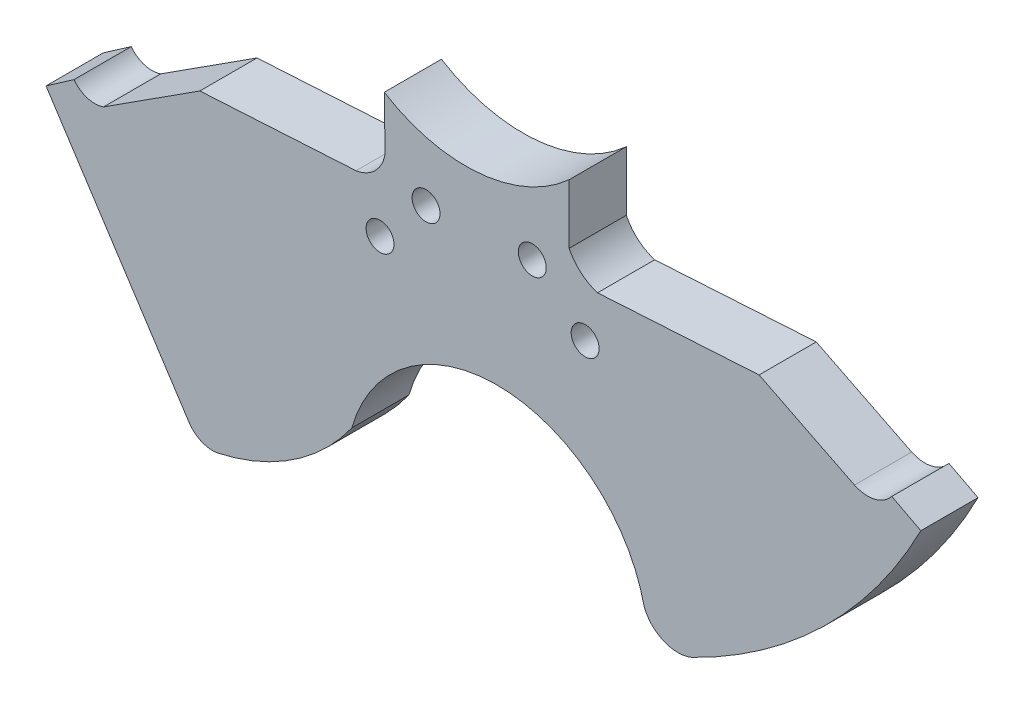
SolidWorks part; units mm, degrees
ref_plane "Plano frontal" through (0, 0, 0) normal (0, 0, 1) x (1, 0, 0)
ref_plane "Plano superior" through (0, 0, 0) normal (0, 1, 0) x (1, 0, 0)
ref_plane "Plano direito" through (0, 0, 0) normal (1, 0, 0) x (0, 0, -1)
sketch "Esboço1" plane through (0, 0, 0) normal (0, 0, 1) x (1, 0, 0)
  line L0 (80.0166, 93.0122) -> (121.8389, 95.564) construction
  line L1 (35.3852, 10.0755) -> (3.023, 59.8213)
  line L2 (121.9464, 97.8545) -> (121.9464, 100.8122)
  line L3 (79.93, 94.4157) -> (79.93, 97.029)
  line L4 (9.3896, 64.2413) -> (3.023, 59.8213)
  line L5 (16.1166, 62.2388) -> (37.9957, 76.3106)
  line L8 (37.9957, 76.3106) -> (73.5102, 78.3627)
  line L9 (79.93, 94.4157) -> (80.1405, 85.276)
  line L16 (121.9464, 87.3069) -> (121.9464, 97.8545)
  line L19 (128.4006, 81.7737) -> (165.136, 83.9713)
  line L21 (165.136, 83.9713) -> (186.825, 73.1367)
  line L22 (195.3054, 75.1425) -> (201.9046, 71.6896)
  line L29 (35.6621, 9.6499) -> (35.3852, 10.0755)
  arc A0 (139.0206, 25.2485) -> (72.5465, 27.2443) centre (105.5339, 17.9302) ccw
  arc A1 (79.93, 94.4157) -> (121.9464, 97.8545) centre (98.4335, 126.7379) ccw construction
  arc A2 (41.9708, 7.0338) -> (72.5465, 27.2443) centre (31.1759, 56.5987) ccw
  arc A3 (41.9708, 7.0338) -> (35.6621, 9.6499) centre (40.8966, 13.3581) cw
  arc A4 (42.6325, 7.1825) -> (41.9708, 7.0338) centre (40.8966, 13.3581) cw construction
  circle A5 centre (89.4219, 79.4375) radius 3.175
  arc A6 (73.5102, 78.3627) -> (80.1405, 85.276) centre (72.2932, 86.166) ccw
  arc A7 (128.4006, 81.7737) -> (121.9464, 87.3069) centre (131.6215, 92.0615) cw
  arc A8 (186.825, 73.1367) -> (195.3054, 75.1425) centre (189.8122, 79.4375) ccw
  arc A9 (150.8125, 21.1901) -> (201.9046, 71.6896) centre (99.1919, 124.5121) ccw
  circle A10 centre (113.5726, 80.8498) radius 3.175
  circle A11 centre (78.9651, 68.1798) radius 3.175
  circle A12 centre (125.5909, 70.9466) radius 3.175
  arc A13 (79.93, 97.029) -> (121.9464, 100.8122) centre (98.4335, 126.7379) ccw
  arc A15 (139.0206, 25.2485) -> (149.8137, 20.6971) centre (146.6721, 28.3201) ccw
  arc A16 (138.4797, 27.3901) -> (139.0206, 25.2485) centre (146.6721, 28.3201) ccw construction
  arc A22 (72.5465, 27.2443) -> (78.9651, 39.5871) centre (31.1759, 56.5987) ccw construction
  arc A24 (9.3896, 64.2413) -> (16.1166, 62.2388) centre (14.1117, 67.8039) ccw
  arc A27 (149.8137, 20.6971) -> (150.8125, 21.1901) centre (99.1919, 124.5121) ccw
  arc A28 (149.8137, 20.6971) -> (150.8125, 21.1901) centre (146.6721, 28.3201) ccw construction
  arc A29 (35.6621, 9.6499) -> (35.3852, 10.0755) centre (40.8966, 13.3581) cw construction
  point P2 (73.6764, 30.5801)
  point P3 (99.3264, 51.6405)
  point P4 (139.0206, 25.2485)
  point P5 (33.989, 12.2217)
  point P8 (19.0282, 35.2654)
  point P9 (5.0558, 56.6965)
  point P10 (32.5703, 72.8212)
  point P11 (42.6325, 7.1825)
  point P12 (113.5726, 80.8498)
  point P13 (89.4219, 79.4375)
  point P14 (99.7059, 89.5158)
  point P15 (119.4422, 95.985)
  point P16 (35.3852, 10.0755)
  point P17 (81.2448, 93.6978)
  point P18 (59.9806, 14.8435)
  point P19 (69.9442, 23.8843)
  point P21 (11.8372, 62.3434)
  point P24 (3.7742, 60.3429)
  point P25 (38.0195, 7.6246)
  point P29 (78.9651, 68.1798)
  point P32 (8.7443, 63.7933)
  point P33 (9.2271, 64.1509)
  point P34 (16.1166, 62.2388)
  point P35 (38.0195, 76.376)
  point P36 (18.6454, 63.6498)
  point P37 (125.5909, 70.9466)
  point P39 (64.8092, 77.8599)
  point P40 (132.1642, 81.9988)
  point P41 (162.9864, 83.8427)
  point P42 (80.1405, 85.276)
  point P45 (121.9464, 87.3069)
  point P46 (80.0013, 91.3187)
  point P47 (73.5102, 78.3627)
  point P50 (43.0748, 76.6041)
  point P52 (77.8481, 80.5521)
  point P60 (128.4006, 81.7737)
  point P61 (121.9464, 94.6427)
  point P66 (169.5352, 81.7737)
  point P67 (124.5296, 83.9425)
  point P71 (186.825, 73.1367)
  point P72 (200.7463, 72.2957)
  point P73 (192.0244, 72.8247)
  point P76 (196.5569, 74.4877)
  point P77 (195.3054, 75.1425)
  point P78 (181.7357, 43.7245)
  point P84 (198.0874, 64.848)
  point P86 (152.8858, 22.2522)
  point P94 (149.8137, 20.6971)
  point P95 (143.929, 20.5448)
  point P101 (9.3896, 64.2413)
extrude "Ressalto-extrusão1" add sketch "Esboço1" along normal blind 13
cosmetic thread "Representação de rosca1"
cosmetic thread "Representação de rosca2"
